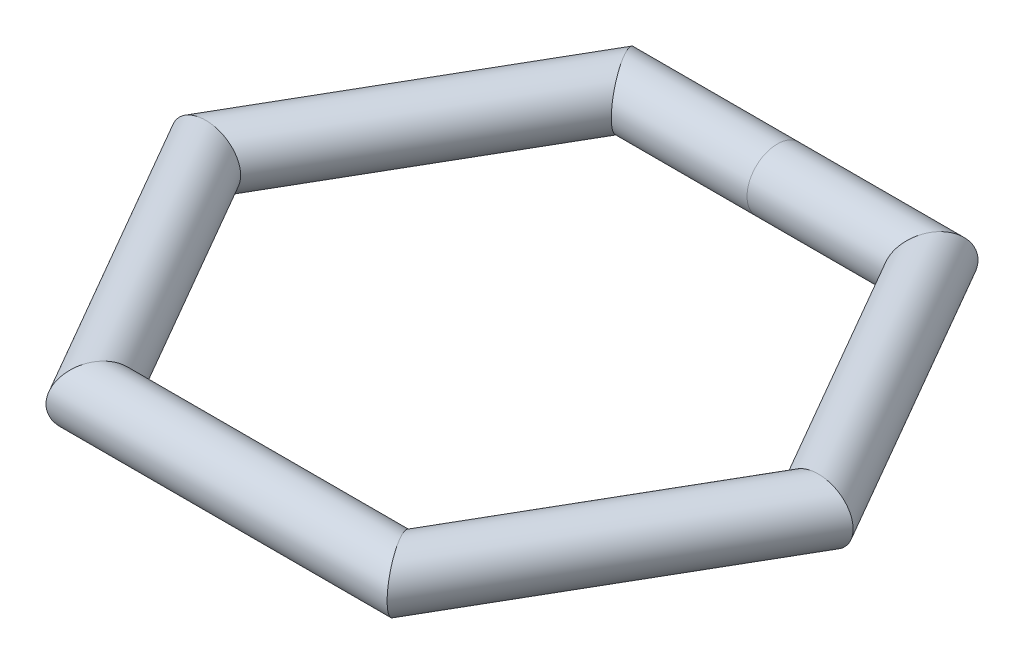
SolidWorks part; units mm, degrees
ref_plane "Front Plane" through (0, 0, 0) normal (0, 0, 1) x (1, 0, 0)
ref_plane "Top Plane" through (0, 0, 0) normal (0, 1, 0) x (1, 0, 0)
ref_plane "Right Plane" through (0, 0, 0) normal (1, 0, 0) x (0, 0, -1)
sketch "Sketch1" plane through (0, 0, 0) normal (0, 1, 0) x (1, 0, 0)
  line L0 (0, 0) -> (0, 71.1788) construction
  line L1 (41.0951, 71.1788) -> (-41.0951, 71.1788)
  line L2 (-41.0951, 71.1788) -> (-82.1902, 0)
  line L3 (-82.1902, 0) -> (-41.0951, -71.1788)
  line L4 (-41.0951, -71.1788) -> (41.0951, -71.1788)
  line L5 (41.0951, -71.1788) -> (82.1902, 0)
  line L6 (82.1902, 0) -> (41.0951, 71.1788)
  circle A0 centre (0, 0) radius 71.1788 construction
  point P1 (-50.0677, 63.7055)
sketch "Sketch2" plane through (0, 0, 0) normal (1, 0, 0) x (0, 0, -1)
  circle A0 centre (71.1788, 0) radius 8.1073
sweep "Sweep1" add profiles "Sketch2" path "Sketch1"
